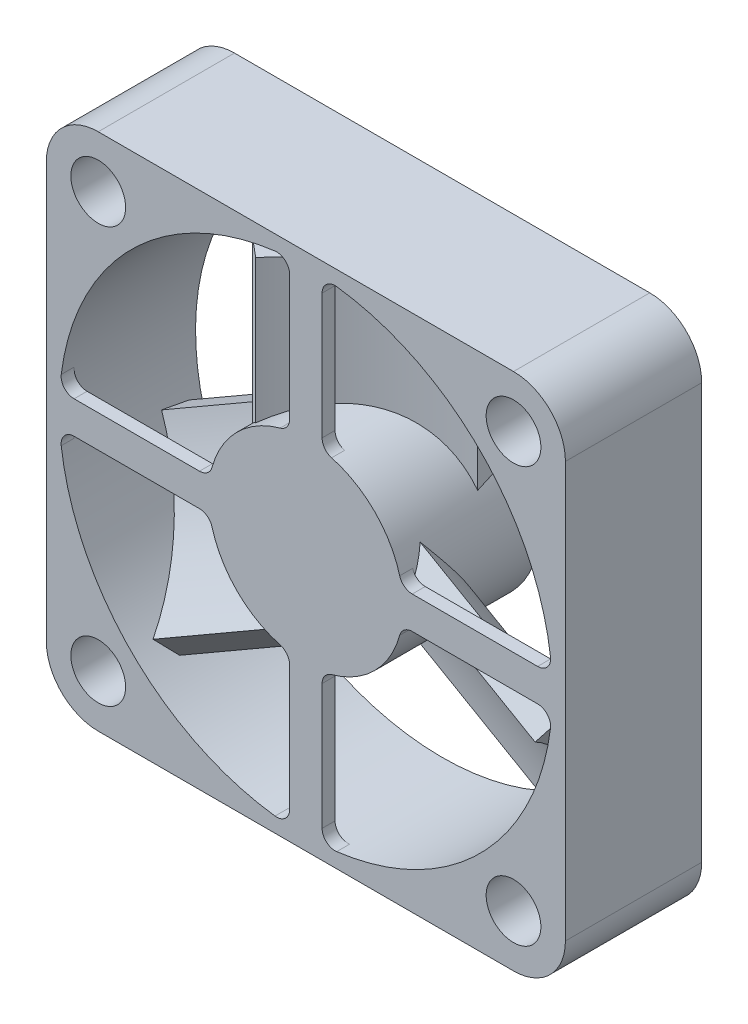
SolidWorks part; units mm, degrees
ref_plane "Front Plane" through (0, 0, 0) normal (0, 0, 1) x (1, 0, 0)
ref_plane "Top Plane" through (0, 0, 0) normal (0, 1, 0) x (1, 0, 0)
ref_plane "Right Plane" through (0, 0, 0) normal (1, 0, 0) x (0, 0, -1)
sketch "Sketch1" plane through (0, 0, 0) normal (0, 0, 1) x (1, 0, 0)
  line L0 (-16, 16) -> (16, -16) construction
  line L1 (-16, 20) -> (16, 20)
  line L2 (-20, 16) -> (-20, -16)
  line L3 (-16, -20) -> (16, -20)
  line L4 (20, 16) -> (20, -16)
  line L5 (-20, 0) -> (0, 0) construction
  line L6 (0, 0) -> (0, 20) construction
  circle A0 centre (0, 0) radius 19
  circle A1 centre (-16, 16) radius 2.11
  circle A2 centre (-16, -16) radius 2.11
  circle A3 centre (16, -16) radius 2.11
  circle A4 centre (16, 16) radius 2.11
  arc A5 (16, 20) -> (20, 16) centre (16, 16) cw
  arc A6 (16, -20) -> (20, -16) centre (16, -16) ccw
  arc A7 (-20, -16) -> (-16, -20) centre (-16, -16) ccw
  arc A8 (-16, 20) -> (-20, 16) centre (-16, 16) ccw
  dimension "D1" = 4
  dimension "D4" = 38
  dimension "D5" = 4.22
  dimension "D2" = 40
  dimension "D3" = 32
  dimension "D6" = 32
extrude "Boss-Extrude1" add sketch "Sketch1" along normal blind 10.5
sketch "Sketch2" plane through (0, 0, 10.5) normal (0, 0, 1) x (1, 0, 0)
  line L0 (-1.25, 17.8588) -> (-1.25, 8.1968)
  line L1 (1.25, 17.8588) -> (1.25, 8.1968)
  line L2 (-1.25, 13.0278) -> (1.25, 13.0278) construction
  line L3 (0, 13.0278) -> (0, 0) construction
  arc A0 (-1.9853, 7.2325) -> (1.9853, 7.2325) centre (0, 0) ccw
  circle A1 centre (0, 0) radius 19 construction
  arc A2 (2.375, 18.851) -> (-2.375, 18.851) centre (0, 0) ccw
  arc A3 (1.25, 8.1968) -> (1.9853, 7.2325) centre (2.25, 8.1968) ccw
  arc A4 (2.375, 18.851) -> (1.25, 17.8588) centre (2.25, 17.8588) ccw
  arc A5 (-1.25, 17.8588) -> (-2.375, 18.851) centre (-2.25, 17.8588) ccw
  arc A6 (-1.25, 8.1968) -> (-1.9853, 7.2325) centre (-2.25, 8.1968) cw
  dimension "D1" = 15
  dimension "D2" = 1
  dimension "D3" = 2.5
extrude "Boss-Extrude2" add sketch "Sketch2" against normal blind 1
pattern_circular "CirPattern1" count 4 over 360 about axis through (0, 0, 0) along (0, 0, 1) of "Boss-Extrude2"
sketch "Sketch4" plane through (0, 0, 9.5) normal (0, 0, -1) x (-1, 0, 0)
  circle A0 centre (0, 0) radius 7.5
extrude "Boss-Extrude3" add sketch "Sketch4" along normal up to surface (9.5 mm away) up to face at (18.11, -16, 0)
sketch "Sketch5" plane through (0, 0, 0) normal (0, 1, 0) x (1, 0, 0)
  arc A0 (-6.0736, -8.5435) -> (6.1313, -1.7058) centre (9.0045, -21.1457) cw
extrude "Extrude-Thin1" add sketch "Sketch5" along normal blind 17 thin
pattern_circular "CirPattern2" count 3 over 360 about axis through (0, 0, 0) along (0, 0, 1) of "Extrude-Thin1"
sketch "Sketch6" plane through (0, 0, 0) normal (0, 0, -1) x (-1, 0, 0)
  line L0 (-16, 16) -> (0, 0) construction
  line L1 (-16.8966, 19.3461) -> (-19.3461, 16.8966)
  line L2 (-19.3461, 16.8966) -> (-18.4495, 13.5505)
  line L3 (-18.4495, 13.5505) -> (-15.1034, 12.6539)
  line L4 (-15.1034, 12.6539) -> (-12.6539, 15.1034)
  line L5 (-12.6539, 15.1034) -> (-13.5505, 18.4495)
  line L6 (-13.5505, 18.4495) -> (-16.8966, 19.3461)
  circle A0 centre (-16, 16) radius 3 construction
  dimension "D1" = 6
extrude "Cut-Extrude1" cut sketch "Sketch6" against normal blind 3.7
pattern_circular "CirPattern3" count 4 over 360 about axis through (0, 0, 0) along (0, 0, 1) of "Cut-Extrude1"
